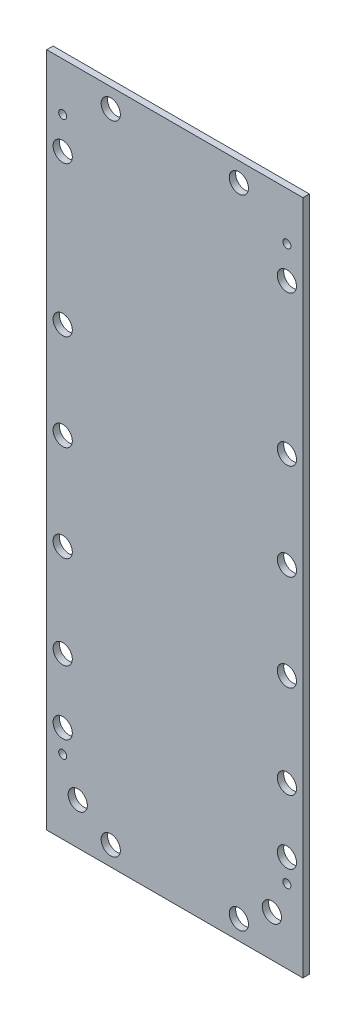
SolidWorks part; units mm, degrees
ref_plane "Front Plane" through (0, 0, 0) normal (0, 0, 1) x (1, 0, 0)
ref_plane "Top Plane" through (0, 0, 0) normal (0, 1, 0) x (1, 0, 0)
ref_plane "Right Plane" through (0, 0, 0) normal (1, 0, 0) x (0, 0, -1)
sketch "Sketch2" plane through (0, 0, 0) normal (0, 0, 1) x (1, 0, 0)
  line L0 (0, 0) -> (0, 211)
  line L1 (0, 211) -> (80, 211)
  line L2 (80, 211) -> (80, 0)
  line L3 (80, 0) -> (0, 0)
extrude "Boss-Extrude1" add sketch "Sketch2" along normal blind 2
sketch "Sketch3" plane through (0, 0, 0) normal (0, 0, -1) x (-1, 0, 0)
  line L0 (-80, 196) -> (0, 196) construction
  line L1 (-80, 0) -> (-80, 211) construction
  line L2 (0, 211) -> (0, 0) construction
  line L3 (-80, 23) -> (0, 23) construction
  line L4 (-75, 211) -> (-75, 0) construction
  line L5 (-80, 211) -> (0, 211) construction
  line L6 (0, 0) -> (-80, 0) construction
  line L7 (-5, 211) -> (-5, 0) construction
  line L8 (-40, 211) -> (-40, 0) construction
  dimension "D1" = 23
  dimension "D2" = 15
  dimension "D3" = 35
  dimension "70" = 70
hole_wizard "M3x0.5 Tapped Hole1" positions "Sketch4" profile "Sketch6" tap size "M3x0.5" standard "ANSI Metric"
sketch "Sketch4" plane through (0, 0, 0) normal (0, 0, -1) x (-1, 0, 0)
  line L0 (-80, 196) -> (0, 196) construction
  line L1 (-75, 211) -> (-75, 0) construction
  line L2 (-5, 211) -> (-5, 0) construction
  line L3 (-80, 23) -> (0, 23) construction
  point P0 (-75, 196)
  point P6 (-5, 196)
  point P10 (-75, 23)
  point P14 (-5, 23)
sketch "Sketch6" plane through (75, 196, 0) normal (1, 0, 0) x (0, 1, 0)
  line L0 (0, 0) -> (0, 10.7511)
  line L1 (0, 10.7511) -> (1.25, 10)
  line L2 (1.25, 10) -> (1.25, 0)
  line L5 (1.25, 0) -> (0, 0)
  line L10 (0, 10.7511) -> (-1.25, 10) construction
  line L11 (0, -6.35) -> (0, 107.95) construction
  dimension "Tap Drill Dia." = 2.5
  dimension "Tap Drill Depth" = 10
  dimension "Drill Angle" = 118
sketch "Sketch7" plane through (0, 0, 0) normal (0, 0, -1) x (-1, 0, 0)
  line L0 (-75, 211) -> (-75, 0) construction
  line L1 (-80, 211) -> (0, 211) construction
  line L2 (0, 0) -> (-80, 0) construction
  line L3 (-5, 211) -> (-5, 0) construction
  line L4 (-40, 211) -> (-40, 0) construction
  line L5 (-80, 0) -> (-80, 211) construction
  line L6 (0, 211) -> (0, 0) construction
  circle A0 centre (-75, 186) radius 3
  circle A1 centre (-75, 139.2) radius 3
  circle A2 centre (-75, 109.2) radius 3
  circle A3 centre (-75, 79.2) radius 3
  circle A4 centre (-75, 50.2) radius 3
  circle A5 centre (-75, 30.2) radius 3
  circle A6 centre (-5, 186) radius 3
  circle A7 centre (-5, 139.2) radius 3
  circle A8 centre (-5, 109.2) radius 3
  circle A9 centre (-5, 79.2) radius 3
  circle A10 centre (-5, 50.2) radius 3
  circle A11 centre (-5, 30.2) radius 3
  circle A12 centre (-70.3, 13) radius 3
  circle A13 centre (-60, 205) radius 3
  circle A14 centre (-20, 205) radius 3
  circle A15 centre (-60, 6) radius 3
  circle A16 centre (-20, 6) radius 3
  circle A17 centre (-9.7, 13) radius 3
  dimension "D4" = 6
  dimension "D10" = 40
  dimension "D1" = 70
  dimension "D2" = 35
  dimension "D3" = 25
  dimension "D5" = 46.8
  dimension "D6" = 30
  dimension "D7" = 30
  dimension "D8" = 29
  dimension "D9" = 20
  dimension "D11" = 20
  dimension "D12" = 6
  dimension "D13" = 6
  dimension "D14" = 9.7
  dimension "D15" = 9.7
  dimension "D16" = 13
extrude "Cut-Extrude1" cut sketch "Sketch7" against normal up to surface (2 mm away) up to face at (73.75, 196, 2)
